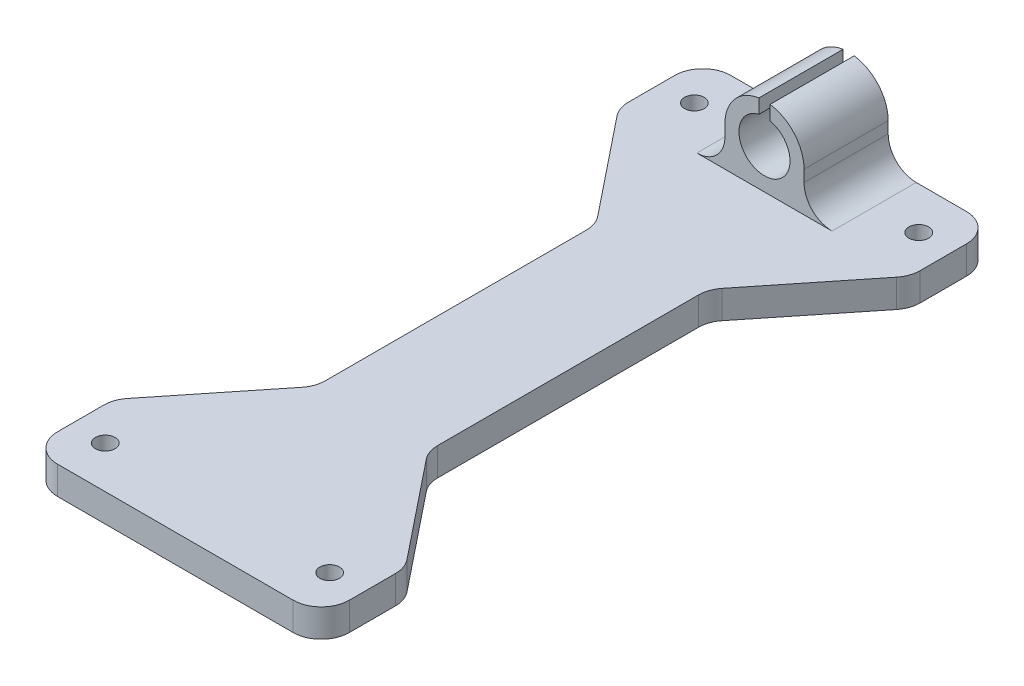
SolidWorks part; units mm, degrees
material "ABS"
ref_plane "Front Plane" through (0, 0, 0) normal (0, 0, 1) x (1, 0, 0)
ref_plane "Top Plane" through (0, 0, 0) normal (0, 1, 0) x (1, 0, 0)
ref_plane "Right Plane" through (0, 0, 0) normal (1, 0, 0) x (0, 0, -1)
sketch "Sketch2" plane through (0, 0, 0) normal (0, 1, 0) x (1, 0, 0)
  line L0 (0, 7.5) -> (52, 7.5) construction
  line L1 (0, 0) -> (52, 0)
  line L2 (0, 0) -> (0, 120)
  line L3 (0, 120) -> (52, 120)
  line L4 (52, 0) -> (52, 120)
  line L5 (52, 60) -> (0, 60) construction
  circle A0 centre (6, 7.5) radius 1.75
  circle A1 centre (46, 7.5) radius 1.75
  circle A2 centre (6, 112.5) radius 1.75
  circle A3 centre (46, 112.5) radius 1.75
  point P17 (48.8017, 0)
  dimension "D1" = 3.5
  dimension "D4" = 40
  dimension "D5" = 6
  dimension "D6" = 6
  dimension "D2" = 7.5
  dimension "D3" = 120
extrude "Boss-Extrude1" add sketch "Sketch2" along normal blind 5
sketch "Sketch3" plane through (0, 5, 0) normal (0, 1, 0) x (1, 0, 0)
  line L0 (0, 105) -> (16, 85)
  line L1 (0, 120) -> (0, 0) construction
  line L2 (16, 85) -> (16, 35)
  line L3 (16, 35) -> (0, 15)
  line L4 (26, 120) -> (26, 0) construction
  line L5 (52, 120) -> (0, 120) construction
  line L6 (0, 0) -> (52, 0) construction
  line L7 (52, 105) -> (36, 85)
  line L8 (36, 85) -> (36, 35)
  line L9 (36, 35) -> (52, 15)
  line L10 (16, 60) -> (26, 60) construction
  line L11 (26, 60) -> (36, 60) construction
  line L14 (0, 105) -> (0, 15)
  line L15 (52, 15) -> (52, 105)
  dimension "D1" = 15
  dimension "D2" = 20
  dimension "D3" = 50
extrude "Cut-Extrude1" cut sketch "Sketch3" against normal through all
sketch "Sketch4" plane through (0, 0, -120) normal (0, 0, -1) x (-1, 0, 0)
  line L0 (-26, 5) -> (-26, 12.05) construction
  line L1 (-52, 5) -> (0, 5) construction
  line L2 (-33.05, 12.05) -> (-33.05, 5)
  line L3 (-18.95, 12.05) -> (-18.95, 5)
  line L4 (-18.95, 5) -> (-33.05, 5)
  circle A0 centre (-26, 12.05) radius 4.55
  arc A1 (-18.95, 12.05) -> (-33.05, 12.05) centre (-26, 12.05) ccw
  dimension "D1" = 9.1
  dimension "D2" = 2.5
extrude "Boss-Extrude2" add sketch "Sketch4" against normal blind 15
sketch "Sketch5" plane through (0, 0, -120) normal (0, 0, -1) x (-1, 0, 0)
  line L0 (-26, 19.1) -> (-26, 0) construction
  line L1 (-52, 0) -> (0, 0) construction
  line L3 (-27, 19.1) -> (-25, 19.1)
  line L4 (-27, 19.1) -> (-27, 16.4887)
  line L5 (-27, 16.4887) -> (-25, 16.4887)
  line L6 (-25, 19.1) -> (-25, 16.4887)
  line L7 (-27, 19.1) -> (-25, 16.4887) construction
  line L8 (-27, 16.4887) -> (-25, 19.1) construction
  arc A0 (-18.95, 12.05) -> (-33.05, 12.05) centre (-26, 12.05) ccw construction
  circle A1 centre (-26, 12.05) radius 4.55 construction
  point P7 (-26, 17.7944)
  point P14 (-25.1056, 19.2438)
  dimension "D1" = 2
extrude "Cut-Extrude2" cut sketch "Sketch5" against normal through all
fillet "Fillet1" radius 5 14 edges at (33.05, 5, -112.5) (18.95, 5, -112.5) (16, 2.5, -85) (16, 2.5, -35) (0, 2.5, -15) (0, 2.5, 0) (52, 2.5, 0) (52, 2.5, -15) (36, 2.5, -35) (36, 2.5, -85) (52, 2.5, -105) (52, 2.5, -120) (0, 2.5, -105) (0, 2.5, -120)
